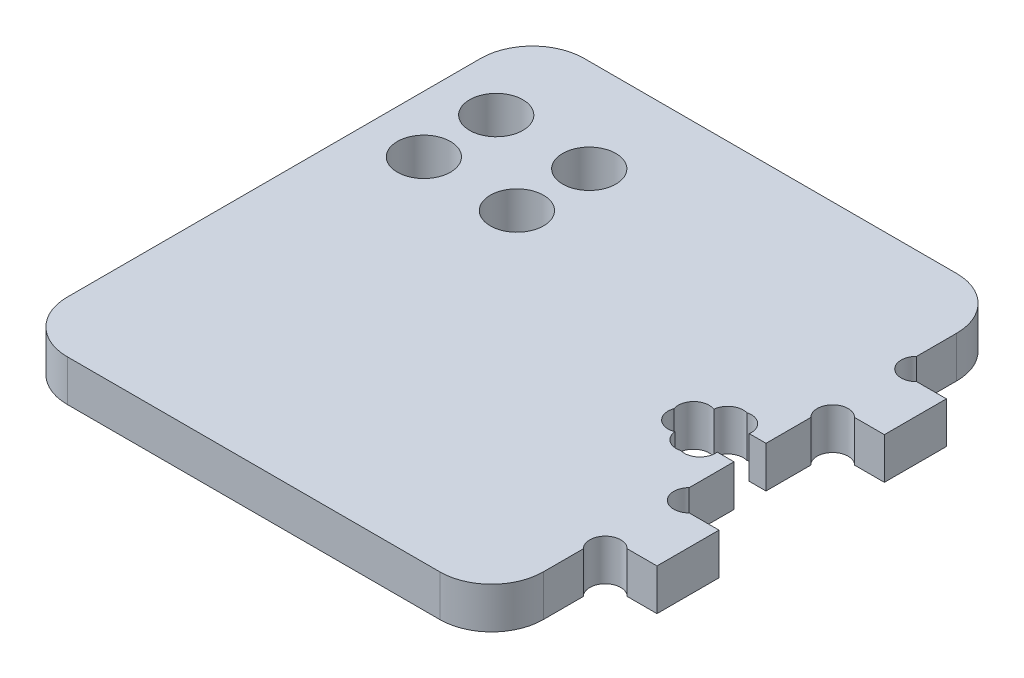
SolidWorks part; units mm, degrees
ref_plane "Alzado" through (0, 0, 0) normal (0, 0, 1) x (1, 0, 0)
ref_plane "Planta" through (0, 0, 0) normal (0, 1, 0) x (1, 0, 0)
ref_plane "Vista lateral" through (0, 0, 0) normal (1, 0, 0) x (0, 0, -1)
sketch "Croquis1" plane through (0, 0, 0) normal (0, 1, 0) x (1, 0, 0)
  line L0 (25.525, 14) -> (25.525, -14) construction
  line L1 (-18.025, -25) -> (18.025, -25)
  line L2 (-23.025, -20) -> (-23.025, 20)
  line L3 (-18.025, 25) -> (18.025, 25)
  line L4 (23.025, -20) -> (23.025, -14)
  line L5 (-23.025, -25) -> (23.025, 25) construction
  line L6 (-23.025, 25) -> (23.025, -25) construction
  line L7 (23.025, 14) -> (28.025, 14)
  line L8 (23.025, -8) -> (23.025, -1.55)
  line L9 (23.025, 8) -> (28.025, 8)
  line L10 (28.025, 14) -> (28.025, 8)
  line L11 (23.025, -8) -> (28.025, -8)
  line L12 (28.025, 11) -> (8.3263, 11) construction
  line L13 (23.025, -14) -> (28.025, -14)
  line L14 (28.025, -8) -> (28.025, -14)
  line L15 (0, 0) -> (25.525, 0) construction
  line L16 (23.025, 14) -> (23.025, 20)
  line L17 (20.975, -1.55) -> (20.975, -2.8)
  line L18 (18.075, 2.8) -> (20.975, 2.8)
  line L19 (18.075, 2.8) -> (18.075, 1.55)
  line L20 (18.075, -2.8) -> (20.975, -2.8)
  line L21 (20.975, 2.8) -> (20.975, 1.55)
  line L22 (16.025, 1.55) -> (18.075, 1.55)
  line L23 (16.025, 1.55) -> (16.025, -1.55)
  line L24 (16.025, -1.55) -> (18.075, -1.55)
  line L25 (23.025, 1.55) -> (23.025, 8)
  line L26 (20.975, 1.55) -> (23.025, 1.55)
  line L27 (18.075, -1.55) -> (18.075, -2.8)
  line L28 (20.975, -1.55) -> (23.025, -1.55)
  line L29 (16.025, 0) -> (0, 0) construction
  line L30 (19.525, 2.8) -> (19.525, -2.8) construction
  line L31 (19.525, 0) -> (16.025, 0) construction
  arc A0 (-18.025, -25) -> (-23.025, -20) centre (-18.025, -20) cw
  arc A1 (18.025, -25) -> (23.025, -20) centre (18.025, -20) ccw
  arc A2 (18.025, 25) -> (23.025, 20) centre (18.025, 20) cw
  arc A3 (-23.025, 20) -> (-18.025, 25) centre (-18.025, 20) cw
  point P0 (0, 0)
  dimension "D3" = 5
  dimension "D4" = 6
  dimension "D1" = 50
  dimension "D2" = 46.05
  dimension "D5" = 5
  dimension "D6" = 14
  dimension "D7" = 3.1
  dimension "D8" = 5.6
  dimension "D9" = 2.9
  dimension "D10" = 7
  dimension "D11" = 3.5
extrude "Saliente-Extruir1" add sketch "Croquis1" along normal blind 4
sketch "Croquis4" plane through (0, 0, 0) normal (0, 1, 0) x (1, 0, 0)
  line L1 (8.4, 26.5) -> (14.55, 26.5)
  line L2 (8.4, 26.5) -> (8.4, -26.5)
  line L3 (8.4, -26.5) -> (14.55, -26.5)
  line L4 (14.55, 26.5) -> (14.55, -26.5)
  line L6 (11.475, 26.5) -> (11.475, -26.5) construction
  line L7 (23.025, -20) -> (23.025, -14) construction
  line L8 (18.025, 25) -> (-18.025, 25) construction
  line L9 (-18.025, -25) -> (18.025, -25) construction
  dimension "D1" = 6.15
  dimension "D2" = 11.55
  dimension "D3" = 1.5
  dimension "D4" = 1.5
sketch "Croquis9" plane through (0, 4, 0) normal (0, 1, 0) x (1, 0, 0)
  line L24 (-18.025, -25) -> (18.025, -25)
  line L25 (23.025, -20) -> (23.025, -14)
  line L26 (23.025, -14) -> (28.025, -14)
  line L27 (28.025, -14) -> (28.025, -8)
  line L28 (28.025, -8) -> (23.025, -8)
  line L29 (23.025, -8) -> (23.025, -1.55)
  line L30 (23.025, -1.55) -> (20.975, -1.55)
  line L31 (20.975, -1.55) -> (20.975, -2.8)
  line L32 (20.975, -2.8) -> (18.075, -2.8)
  line L33 (18.075, -2.8) -> (18.075, -1.55)
  line L34 (18.075, -1.55) -> (16.025, -1.55)
  line L35 (16.025, -1.55) -> (16.025, 1.55)
  line L36 (16.025, 1.55) -> (18.075, 1.55)
  line L37 (18.075, 1.55) -> (18.075, 2.8)
  line L38 (18.075, 2.8) -> (20.975, 2.8)
  line L39 (20.975, 2.8) -> (20.975, 1.55)
  line L40 (20.975, 1.55) -> (23.025, 1.55)
  line L41 (23.025, 1.55) -> (23.025, 8)
  line L42 (23.025, 8) -> (28.025, 8)
  line L43 (28.025, 8) -> (28.025, 14)
  line L44 (28.025, 14) -> (23.025, 14)
  line L45 (23.025, 14) -> (23.025, 20)
  line L46 (18.025, 25) -> (-18.025, 25)
  line L47 (-23.025, 20) -> (-23.025, -20)
  line L48 (-18.025, -25) -> (18.025, -25)
  line L49 (23.025, -20) -> (23.025, -14)
  line L50 (23.025, -14) -> (28.025, -14)
  line L51 (28.025, -14) -> (28.025, -8)
  line L52 (28.025, -8) -> (23.025, -8)
  line L53 (23.025, -8) -> (23.025, -1.55)
  line L54 (23.025, -1.55) -> (20.975, -1.55)
  line L55 (20.975, -1.55) -> (20.975, -2.8)
  line L56 (20.975, -2.8) -> (18.075, -2.8)
  line L57 (18.075, -2.8) -> (18.075, -1.55)
  line L58 (18.075, -1.55) -> (16.025, -1.55)
  line L59 (16.025, -1.55) -> (16.025, 1.55)
  line L60 (16.025, 1.55) -> (18.075, 1.55)
  line L61 (18.075, 1.55) -> (18.075, 2.8)
  line L62 (18.075, 2.8) -> (20.975, 2.8)
  line L63 (20.975, 2.8) -> (20.975, 1.55)
  line L64 (20.975, 1.55) -> (23.025, 1.55)
  line L65 (23.025, 1.55) -> (23.025, 8)
  line L66 (23.025, 8) -> (28.025, 8)
  line L67 (28.025, 8) -> (28.025, 14)
  line L68 (28.025, 14) -> (23.025, 14)
  line L69 (23.025, 14) -> (23.025, 20)
  line L70 (18.025, 25) -> (-18.025, 25)
  line L71 (-23.025, 20) -> (-23.025, -20)
  arc A4 (-23.025, -20) -> (-18.025, -25) centre (-18.025, -20) ccw
  arc A5 (18.025, -25) -> (23.025, -20) centre (18.025, -20) ccw
  arc A6 (23.025, 20) -> (18.025, 25) centre (18.025, 20) ccw
  arc A7 (-18.025, 25) -> (-23.025, 20) centre (-18.025, 20) ccw
  arc A8 (-23.025, -20) -> (-18.025, -25) centre (-18.025, -20) ccw
  arc A9 (18.025, -25) -> (23.025, -20) centre (18.025, -20) ccw
  arc A10 (23.025, 20) -> (18.025, 25) centre (18.025, 20) ccw
  arc A11 (-18.025, 25) -> (-23.025, 20) centre (-18.025, 20) ccw
  dimension "D1" = 0
sketch "Croquis6" plane through (0, 4, 0) normal (0, 1, 0) x (1, 0, 0)
  line L0 (16.025, 1.55) -> (18.075, 1.55) construction
  line L1 (16.025, -1.55) -> (16.025, 1.55) construction
  line L2 (18.075, -1.55) -> (16.025, -1.55) construction
  line L3 (16.025, 1.55) -> (17.525, 0.05)
  line L4 (16.025, -1.55) -> (17.525, -0.05)
  line L5 (18.075, 2.8) -> (20.975, 2.8) construction
  line L6 (18.075, 1.55) -> (18.075, 2.8) construction
  line L7 (18.075, 2.8) -> (19.575, 1.3)
  line L8 (20.975, 2.8) -> (20.975, 1.55) construction
  line L9 (20.975, 2.8) -> (19.475, 1.3)
  line L10 (18.075, -2.8) -> (18.075, -1.55) construction
  line L11 (20.975, -2.8) -> (18.075, -2.8) construction
  line L12 (18.075, -2.8) -> (19.575, -1.3)
  line L13 (20.975, -1.55) -> (20.975, -2.8) construction
  line L14 (20.975, -2.8) -> (19.475, -1.3)
  circle A0 centre (17.525, 0.05) radius 1.5
  circle A1 centre (17.525, -0.05) radius 1.5
  circle A2 centre (19.575, -1.3) radius 1.5
  circle A3 centre (19.475, -1.3) radius 1.5
  circle A4 centre (19.475, 1.3) radius 1.5
  circle A5 centre (19.575, 1.3) radius 1.5
  dimension "D1" = 3
sketch "Croquis7" plane through (0, 4, 0) normal (0, 1, 0) x (1, 0, 0)
  line L0 (16.025, 1.55) -> (17.525, 0.05) construction
  line L1 (16.025, -1.55) -> (17.525, -0.05) construction
  line L2 (18.075, -2.8) -> (19.575, -1.3) construction
  line L3 (20.975, -2.8) -> (19.475, -1.3) construction
  line L4 (20.975, 2.8) -> (19.475, 1.3) construction
  line L5 (18.075, 2.8) -> (19.575, 1.3) construction
  line L11 (21.4023, 1.55) -> (23.025, 1.55)
  line L12 (23.025, 1.55) -> (23.025, -1.55)
  line L13 (23.025, -1.55) -> (21.4023, -1.55)
  arc A0 (17.6425, 1.8822) -> (15.6677, 0) centre (17.0857, 0.4893) ccw
  arc A1 (15.6677, 0) -> (17.6425, -1.8822) centre (17.0857, -0.4893) ccw
  arc A2 (17.6425, -1.8822) -> (19.525, -3.1879) centre (19.1357, -1.7393) ccw
  arc A3 (19.525, -3.1879) -> (21.4023, -1.55) centre (19.9143, -1.7393) ccw
  arc A4 (21.4023, 1.55) -> (19.525, 3.1879) centre (19.9143, 1.7393) ccw
  arc A5 (19.525, 3.1879) -> (17.6425, 1.8822) centre (19.1357, 1.7393) ccw
  dimension "D1" = 3
extrude "Cortar-Extruir4" cut sketch "Croquis7" against normal through all
sketch "Croquis10" plane through (0, 4, 0) normal (0, 1, 0) x (1, 0, 0)
  line L0 (0, 0) -> (23.8324, 0) construction
  line L1 (28.025, 14) -> (23.025, 14) construction
  line L2 (23.025, 14) -> (23.025, 20) construction
  line L3 (23.025, 8) -> (28.025, 8) construction
  line L4 (23.025, 1.55) -> (23.025, 8) construction
  line L5 (23.025, 14) -> (24.525, 15.5) construction
  line L7 (23.025, 8) -> (24.525, 6.5) construction
  circle A0 centre (24.525, 15.5) radius 1.5 construction
  circle A1 centre (24.525, 6.5) radius 1.5 construction
  circle A2 centre (24.0857, 15.0607) radius 1.5
  circle A3 centre (24.0857, 6.9393) radius 1.5
  circle A4 centre (24.0857, -15.0607) radius 1.5
  circle A5 centre (24.0857, -6.9393) radius 1.5
  dimension "D1" = 3
extrude "Cortar-Extruir5" cut sketch "Croquis10" against normal through all
sketch "Croquis11" plane through (0, 4, 0) normal (0, 1, 0) x (1, 0, 0)
  line L0 (-16.775, 9) -> (-18.275, 9) construction
  line L1 (-16.775, 7) -> (-18.275, 7)
  line L2 (-16.775, 11) -> (-18.275, 11)
  line L3 (-16.775, 16) -> (-18.275, 16) construction
  line L4 (-16.775, 14) -> (-18.275, 14)
  line L5 (-16.775, 18) -> (-18.275, 18)
  line L6 (-9.275, 9) -> (-7.775, 9) construction
  line L7 (-23.025, 20) -> (-3.025, 20) construction
  line L8 (-23.025, 20) -> (-23.025, 5) construction
  line L9 (-23.025, 5) -> (-3.025, 5) construction
  line L10 (-3.025, 20) -> (-3.025, 5) construction
  line L11 (-17.525, 16) -> (-17.525, 9) construction
  line L12 (-17.525, 12.5) -> (-13.025, 12.5) construction
  line L13 (-13.025, 20) -> (-13.025, 5) construction
  line L14 (-9.275, 7) -> (-7.775, 7)
  line L15 (-9.275, 11) -> (-7.775, 11)
  line L16 (-9.275, 16) -> (-7.775, 16) construction
  line L17 (-9.275, 14) -> (-7.775, 14)
  line L18 (-9.275, 18) -> (-7.775, 18)
  line L19 (18.025, 25) -> (-18.025, 25) construction
  line L21 (-23.025, 20) -> (-23.025, -20) construction
  arc A0 (-16.775, 7) -> (-16.775, 11) centre (-16.775, 9) ccw
  arc A1 (-18.275, 11) -> (-18.275, 7) centre (-18.275, 9) ccw
  arc A2 (-16.775, 14) -> (-16.775, 18) centre (-16.775, 16) ccw
  arc A3 (-18.275, 18) -> (-18.275, 14) centre (-18.275, 16) ccw
  arc A4 (-9.275, 7) -> (-9.275, 11) centre (-9.275, 9) cw
  arc A5 (-7.775, 11) -> (-7.775, 7) centre (-7.775, 9) cw
  arc A6 (-9.275, 14) -> (-9.275, 18) centre (-9.275, 16) cw
  arc A7 (-7.775, 18) -> (-7.775, 14) centre (-7.775, 16) cw
  point P2 (-17.525, 9)
  point P17 (-17.525, 16)
  point P26 (-8.525, 9)
  point P33 (-8.525, 16)
  dimension "D3" = 2
  dimension "D1" = 11
  dimension "D2" = 1.5
  dimension "D4" = 20
  dimension "D5" = 15
  dimension "D6" = 9
  dimension "D7" = 5
sketch "Croquis12" plane through (0, 4, 0) normal (0, 1, 0) x (1, 0, 0)
  circle A0 centre (-17.525, 16) radius 2.575
  circle A1 centre (-8.525, 16) radius 2.575
  circle A2 centre (-8.525, 9) radius 2.575
  circle A3 centre (-17.525, 9) radius 2.575
  dimension "D1" = 5.15
extrude "Cortar-Extruir6" cut sketch "Croquis12" against normal through all
